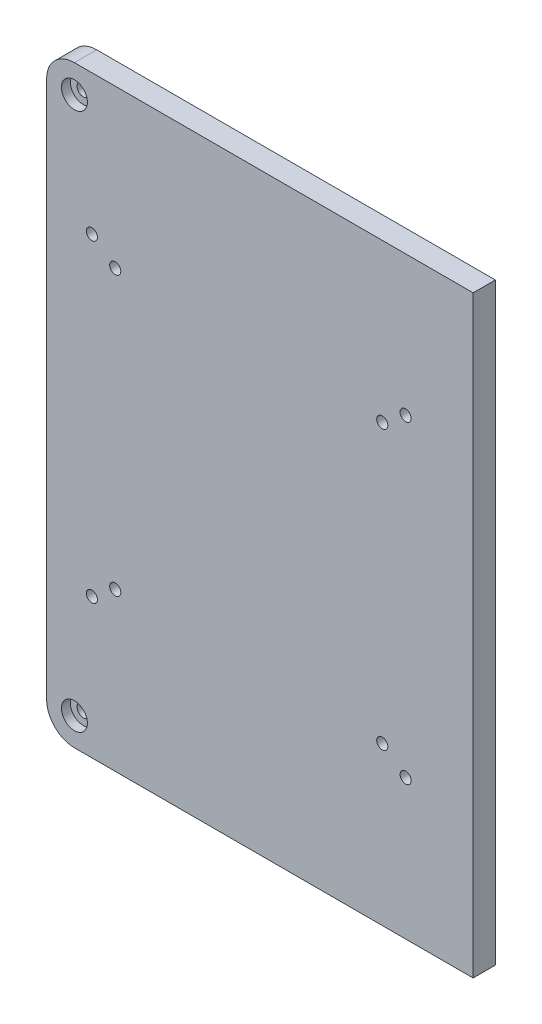
SolidWorks part; units mm, degrees
ref_plane "Front Plane" through (0, 0, 0) normal (0, 0, 1) x (1, 0, 0)
ref_plane "Top Plane" through (0, 0, 0) normal (0, 1, 0) x (1, 0, 0)
ref_plane "Right Plane" through (0, 0, 0) normal (1, 0, 0) x (0, 0, -1)
sketch "Sketch1" plane through (0, 0, 0) normal (0, 0, 1) x (1, 0, 0)
  line L1 (-107.5, 80) -> (107.5, 80)
  line L2 (-115, 72.5) -> (-115, -72.5)
  line L3 (-107.5, -80) -> (107.5, -80)
  line L4 (115, 72.5) -> (115, -72.5)
  line L5 (-115, 80) -> (115, -80) construction
  line L6 (-115, -80) -> (115, 80) construction
  arc A0 (-115, -72.5) -> (-107.5, -80) centre (-107.5, -72.5) ccw
  arc A1 (107.5, -80) -> (115, -72.5) centre (107.5, -72.5) ccw
  arc A2 (107.5, 80) -> (115, 72.5) centre (107.5, 72.5) cw
  arc A3 (-107.5, 80) -> (-115, 72.5) centre (-107.5, 72.5) ccw
  point P0 (0, 0)
  dimension "D3" = 7.5
  dimension "D1" = 230
  dimension "D2" = 160
extrude "Boss-Extrude1" add sketch "Sketch1" along normal blind 6
sketch "Sketch4" plane through (0, 0, 6) normal (0, 0, 1) x (1, 0, 0)
  line L0 (107.5, 80) -> (-107.5, 80) construction
  line L3 (-115, 72.5) -> (-115, -72.5) construction
  line L4 (-107.5, -80) -> (107.5, -80) construction
  circle A0 centre (-96.5, 37.5) radius 1.5
  circle A1 centre (-96.5, -37.5) radius 1.5
  circle A2 centre (-24.5, 37.5) radius 1.5
  circle A3 centre (-24.5, -37.5) radius 1.5
  dimension "D2" = 3
  dimension "D3" = 3
  dimension "D6" = 3
  dimension "D7" = 3
  dimension "D12" = 18.5
  dimension "D1" = 75
  dimension "D4" = 42.5
  dimension "D5" = 18.5
  dimension "D8" = 72
  dimension "D9" = 72
  dimension "D10" = 42.5
  dimension "D11" = 42.5
extrude "Cut-Extrude3" cut sketch "Sketch4" against normal through all
sketch "Sketch5" plane through (0, 0, 6) normal (0, 0, 1) x (1, 0, 0)
  line L0 (-107.5, -80) -> (107.5, -80) construction
  line L1 (107.5, 80) -> (-107.5, 80) construction
  line L2 (115, -72.5) -> (115, 72.5) construction
  circle A0 centre (95, -62.5) radius 1.375
  circle A1 centre (95, 62.5) radius 1.375
  circle A2 centre (41.7, -62.5) radius 1.375
  circle A3 centre (41.7, 62.5) radius 1.375
  dimension "D1" = 125
  dimension "D4" = 2.75
  dimension "D6" = 53.3
  dimension "D7" = 125
  dimension "D8" = 20
  dimension "D9" = 17.5
  dimension "D2" = 17.5
  dimension "D3" = 20
  dimension "D5" = 53.3
extrude "Cut-Extrude4" cut sketch "Sketch5" against normal through all and the other way through all
sketch "Sketch7" plane through (0, 0, 6) normal (0, 0, 1) x (1, 0, 0)
  circle A0 centre (-102.8, 42.3) radius 1.5
  circle A1 centre (-96.5, 37.5) radius 1.5 construction
  circle A2 centre (-102.8, -42.3) radius 1.5
  circle A3 centre (-18.2, -42.3) radius 1.5
  circle A4 centre (-18.2, 42.3) radius 1.5
  circle A5 centre (-96.5, -37.5) radius 1.5 construction
  circle A6 centre (-24.5, -37.5) radius 1.5 construction
  circle A7 centre (-24.5, 37.5) radius 1.5 construction
  dimension "D1" = 6.3
  dimension "D3" = 3
  dimension "D4" = 3
  dimension "D5" = 3
  dimension "D6" = 3
  dimension "D7" = 4.8
  dimension "D8" = 6.3
  dimension "D10" = 4.8
  dimension "D11" = 4.8
  dimension "D12" = 6.3
  dimension "D2" = 4.8
extrude "Cut-Extrude6" cut sketch "Sketch7" against normal through all
sketch "Sketch8" plane through (0, 0, 0) normal (0, 0, -1) x (-1, 0, 0)
  circle A0 centre (18.2, 42.3) radius 3
  circle A1 centre (18.2, -42.3) radius 3
  circle A2 centre (102.8, -42.3) radius 3
  circle A3 centre (102.8, 42.3) radius 3
  dimension "D1" = 6
  dimension "D2" = 6
  dimension "D3" = 6
  dimension "D4" = 6
extrude "Cut-Extrude7" cut sketch "Sketch8" against normal blind 3.5
hole_wizard "CBORE for M3 Pan Head Machine Screw1" positions "Sketch9" profile "Sketch10" counterbore size "M3" standard "ANSI Metric" end condition through all
sketch "Sketch9" plane through (0, 0, 6) normal (0, 0, 1) x (1, 0, 0)
  line L1 (107.5, 80) -> (-107.5, 80) construction
  line L2 (-115, 72.5) -> (-115, -72.5) construction
  line L3 (-107.5, -80) -> (107.5, -80) construction
  line L4 (115, -72.5) -> (115, 72.5) construction
  point P0 (-107.5, 72.5)
  point P2 (-107.5, -72.5)
  point P4 (107.5, -72.5)
  point P6 (107.5, 72.5)
  dimension "D1" = 7.5
  dimension "D2" = 7.5
  dimension "D3" = 7.5
  dimension "D4" = 7.5
  dimension "D5" = 7.5
  dimension "D6" = 7.5
  dimension "D7" = 7.5
  dimension "D8" = 7.5
sketch "Sketch10" plane through (-107.5, 72.5, 6) normal (1, 0, 0) x (0, -1, 0)
  line L0 (0, 0) -> (0, 6)
  line L1 (0, 6) -> (1.7, 6)
  line L3 (1.7, 6) -> (1.7, 2.4)
  line L4 (1.7, 2.4) -> (3.5, 2.4)
  line L5 (3.5, 2.4) -> (3.5, 0)
  line L7 (3.5, 0) -> (0, 0)
  line L11 (0, -6.35) -> (0, 107.95) construction
  dimension "Thru Hole Dia." = 3.4
  dimension "Thru Hole Depth" = 6
  dimension "C'Bore Dia." = 7
  dimension "C'Bore Depth" = 2.4
sketch "Sketch11" plane through (0, 0, 0) normal (0, 0, -1) x (-1, 0, 0)
  line L0 (-115, -72.5) -> (-115, 72.5) construction
  line L1 (0, 80) -> (-115, 80)
  line L2 (0, 80) -> (0, -80)
  line L3 (0, -80) -> (-115, -80)
  line L4 (-115, 80) -> (-115, -80)
  line L5 (-107.5, 80) -> (107.5, 80) construction
  line L6 (107.5, -80) -> (-107.5, -80) construction
  dimension "D1" = 0
  dimension "D2" = 0
  dimension "D3" = 0
  dimension "D4" = 115
extrude "Cut-Extrude8" cut sketch "Sketch11" against normal blind 10
